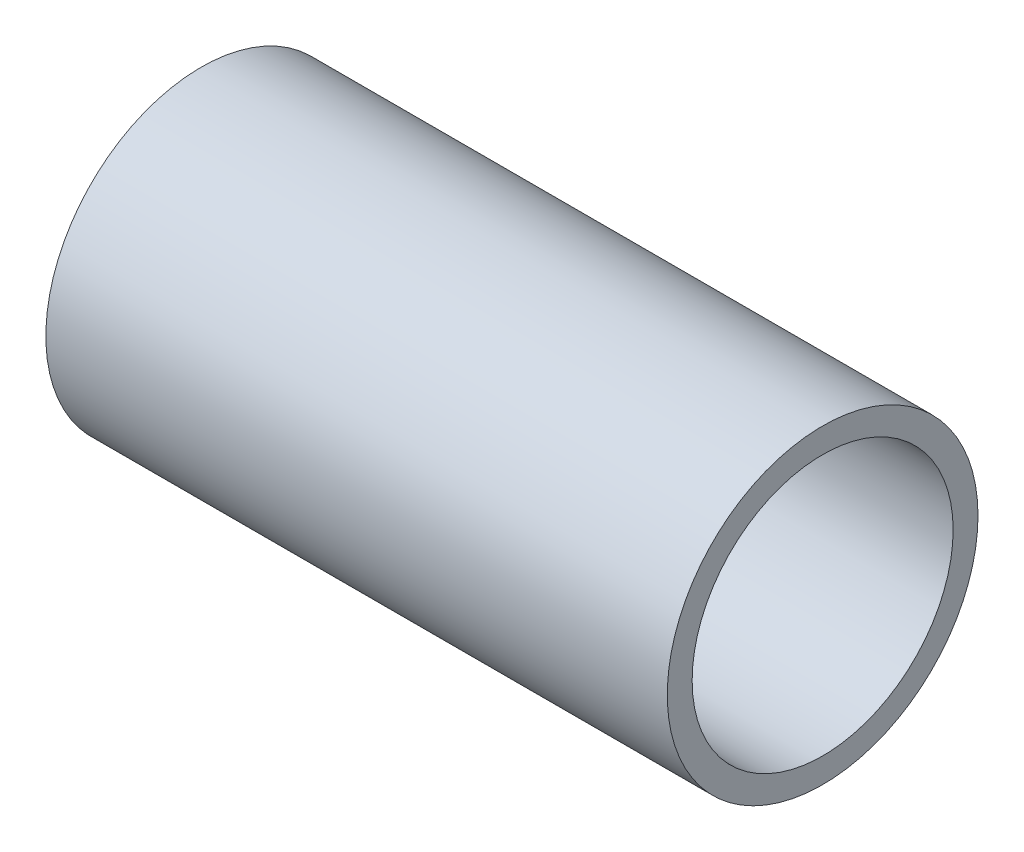
SolidWorks part; units mm, degrees
ref_plane "Front Plane" through (0, 0, 0) normal (0, 0, 1) x (1, 0, 0)
ref_plane "Top Plane" through (0, 0, 0) normal (0, 1, 0) x (1, 0, 0)
ref_plane "Right Plane" through (0, 0, 0) normal (1, 0, 0) x (0, 0, -1)
sketch "Sketch1" plane through (0, 0, 0) normal (1, 0, 0) x (0, 0, -1)
  circle A0 centre (0, 0) radius 9.525
  dimension "D1" = 19.05
extrude "Boss-Extrude1" add sketch "Sketch1" along normal blind 38.1
sketch "Sketch3" plane through (0, 0, 0) normal (-1, 0, 0) x (0, 0, 1)
  circle A0 centre (0, 0) radius 8.509
  dimension "D1" = 17.018
extrude "Cut-Extrude1" cut sketch "Sketch3" against normal blind 1.524
sketch "Sketch4" plane through (1.524, 0, 0) normal (-1, 0, 0) x (0, 0, 1)
  circle A0 centre (0, 0) radius 8.001
  dimension "D1" = 16.002
extrude "Cut-Extrude2" cut sketch "Sketch4" against normal through all
